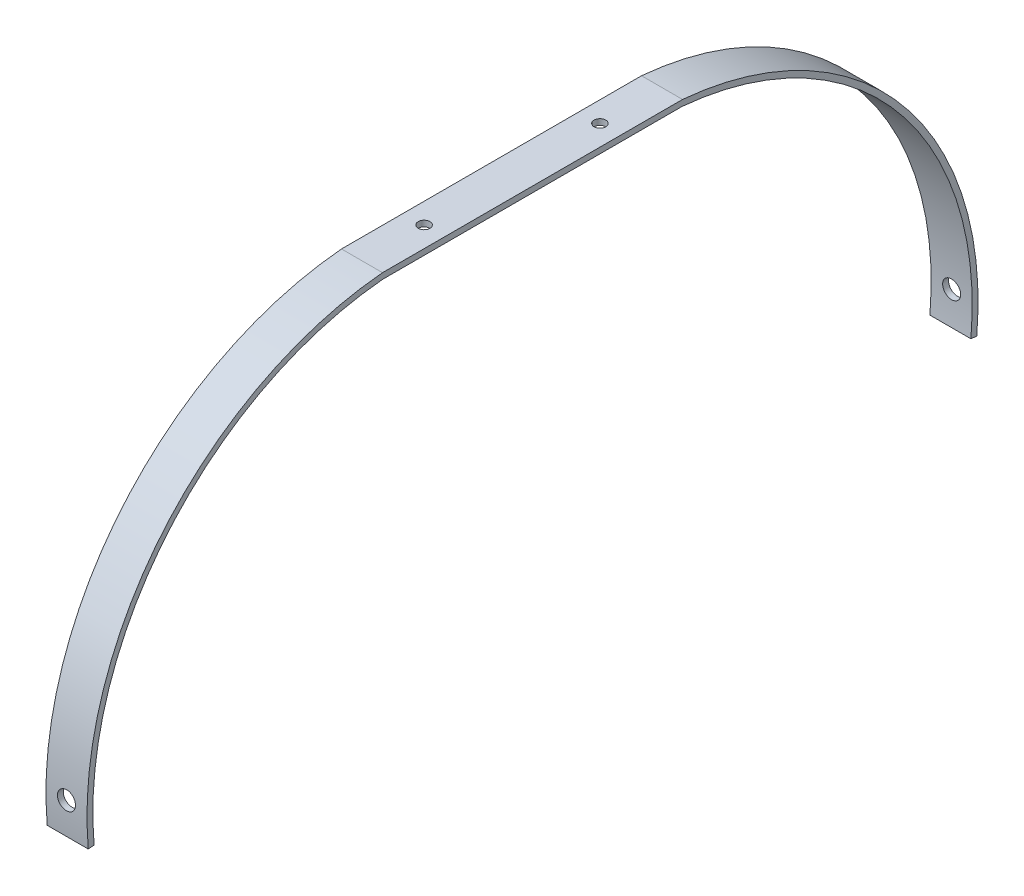
SolidWorks part; units mm, degrees
ref_plane "Front Plane" through (0, 0, 0) normal (0, 0, 1) x (1, 0, 0)
ref_plane "Top Plane" through (0, 0, 0) normal (0, 1, 0) x (1, 0, 0)
ref_plane "Right Plane" through (0, 0, 0) normal (1, 0, 0) x (0, 0, -1)
sketch "Sketch1" plane through (0, 0, 0) normal (1, 0, 0) x (0, 0, -1)
  line L0 (-65, -1.27) -> (-65, -151.27) construction
  line L1 (-65, -1.27) -> (65, -1.27)
  line L2 (-65, -1.27) -> (-65, 1.27)
  line L3 (-65, 1.27) -> (65, 1.27)
  line L4 (65, -1.27) -> (65, 1.27)
  line L5 (-65, -1.27) -> (65, 1.27) construction
  line L6 (-65, 1.27) -> (65, -1.27) construction
  line L7 (-65, -151.27) -> (-192.5, -151.27) construction
  line L8 (0, 0) -> (0, -148.537) construction
  line L9 (-189.9701, -151.0438) -> (-192.5, -151.27)
  line L10 (65, -151.27) -> (192.5, -151.27) construction
  line L11 (189.9701, -151.0438) -> (192.5, -151.27)
  arc A0 (-65, 1.27) -> (-192.5, -151.27) centre (-52.48, -138.75) ccw
  arc A1 (-64.7738, -1.2599) -> (-189.9701, -151.0438) centre (-52.48, -138.75) ccw
  arc A2 (64.7738, -1.2599) -> (189.9701, -151.0438) centre (52.48, -138.75) cw
  arc A3 (65, 1.27) -> (192.5, -151.27) centre (52.48, -138.75) cw
  point P0 (0, 0)
  dimension "D1" = 130
  dimension "D2" = 2.54
  dimension "D3" = 150
  dimension "D4" = 127.5
  dimension "D5" = 2.54
extrude "Boss-Extrude1" add sketch "Sketch1" along normal blind 17.78
sketch "Sketch2" plane through (0, 0, 0) normal (0, 0, 1) x (1, 0, 0)
  line L0 (0, 0) -> (8.89, 0) construction
  line L1 (8.89, 0) -> (8.89, -137.16) construction
  circle A0 centre (8.89, -137.16) radius 3.9142
  dimension "D1" = 8.89
  dimension "D2" = 137.16
extrude "Cut-Extrude1" cut sketch "Sketch2" against normal through all both and the other way through all
sketch "Sketch3" plane through (0, 1.27, 0) normal (0, 1, 0) x (1, 0, 0)
  line L0 (0, 0) -> (17.78, 0) construction
  line L1 (17.78, -65) -> (17.78, 65) construction
  line L2 (8.89, 0) -> (8.89, 38.1) construction
  line L3 (8.89, 0) -> (8.89, -38.1) construction
  circle A0 centre (8.89, 38.1) radius 2.54
  circle A1 centre (8.89, -38.1) radius 2.54
  dimension "D3" = 5.08
  dimension "D4" = 5.08
  dimension "D1" = 38.1
  dimension "D2" = 38.1
extrude "Cut-Extrude2" cut sketch "Sketch3" against normal blind 7.62
